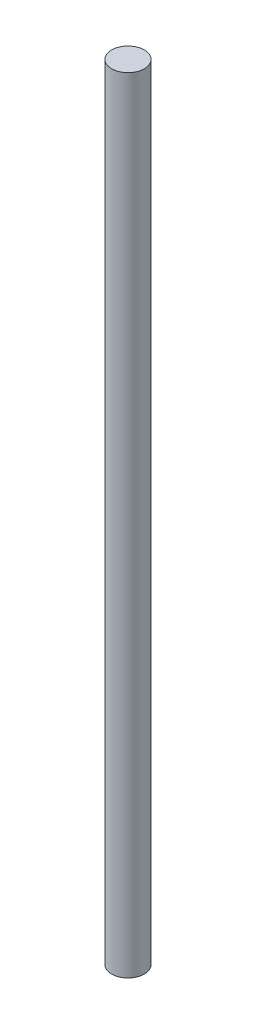
SolidWorks part; units mm, degrees
ref_plane "Front Plane" through (0, 0, 0) normal (0, 0, 1) x (1, 0, 0)
ref_plane "Top Plane" through (0, 0, 0) normal (0, 1, 0) x (1, 0, 0)
ref_plane "Right Plane" through (0, 0, 0) normal (1, 0, 0) x (0, 0, -1)
sketch "Sketch1" plane through (0, 0, 0) normal (0, 1, 0) x (1, 0, 0)
  circle A0 centre (0, 0) radius 4.7625
  dimension "D1" = 9.525
extrude "Boss-Extrude1" add sketch "Sketch1" along normal blind 228.6
